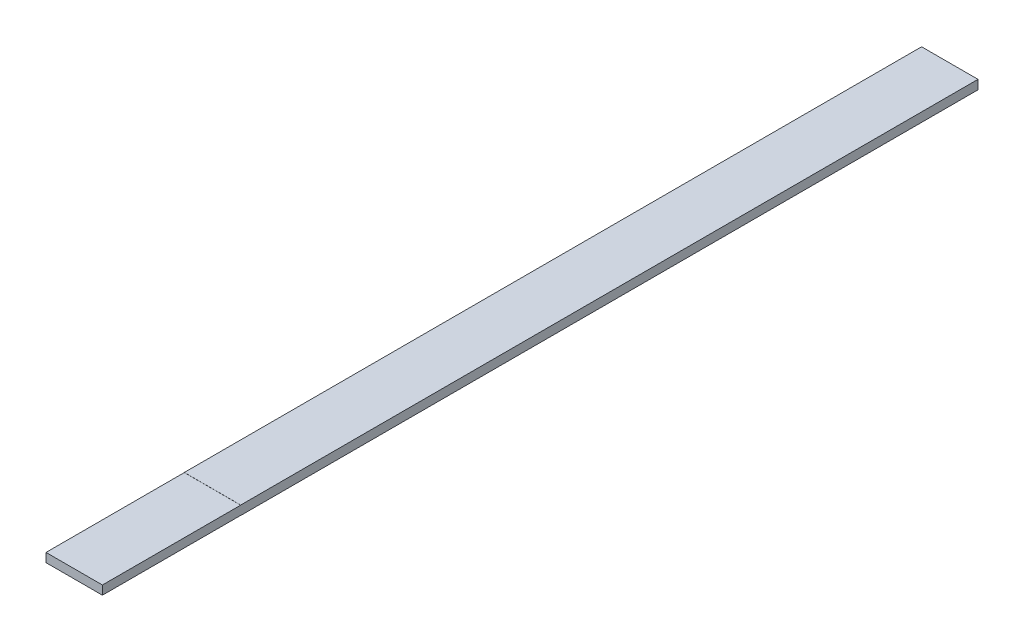
SolidWorks part; units mm, degrees
material "Ultracore Honeycomb"
ref_plane "Front Plane" through (0, 0, 0) normal (0, 0, 1) x (1, 0, 0)
ref_plane "Top Plane" through (0, 0, 0) normal (0, 1, 0) x (1, 0, 0)
ref_plane "Right Plane" through (0, 0, 0) normal (1, 0, 0) x (0, 0, -1)
sketch "Sketch2" plane through (0, 0, 0) normal (0, 0, 1) x (1, 0, 0)
  line L1 (-18, 2.9) -> (18, 2.9)
  line L2 (-18, 2.9) -> (-18, -2.9)
  line L3 (-18, -2.9) -> (18, -2.9)
  line L4 (18, 2.9) -> (18, -2.9)
  line L5 (-18, 2.9) -> (18, -2.9) construction
  line L6 (-18, -2.9) -> (18, 2.9) construction
  point P0 (0, 0)
  dimension "D1" = 36
  dimension "D2" = 5.8
extrude "Boss-Extrude1" add sketch "Sketch2" along normal blind 558.8
sketch "Sketch3" plane through (18, 0, 0) normal (1, 0, 0) x (0, 0, -1)
  line L0 (-470.55, 2.8314) -> (-470.55, -2.8314) construction
  line L1 (-558.8, -2.9) -> (-470.55, -2.9)
  line L2 (-558.8, -2.9) -> (-558.8, -2.8314)
  line L3 (-558.8, -2.8314) -> (-470.55, -2.8314)
  line L4 (-470.55, -2.9) -> (-470.55, -2.8314)
  line L5 (-558.8, 2.9) -> (-470.55, 2.9)
  line L6 (-558.8, 2.9) -> (-558.8, 2.8314)
  line L7 (-558.8, 2.8314) -> (-470.55, 2.8314)
  line L8 (-470.55, 2.9) -> (-470.55, 2.8314)
  dimension "D1" = 88.25
  dimension "D2" = 0.0686
  dimension "D3" = 0.0686
extrude "Cut-Extrude1" cut sketch "Sketch3" against normal through all
